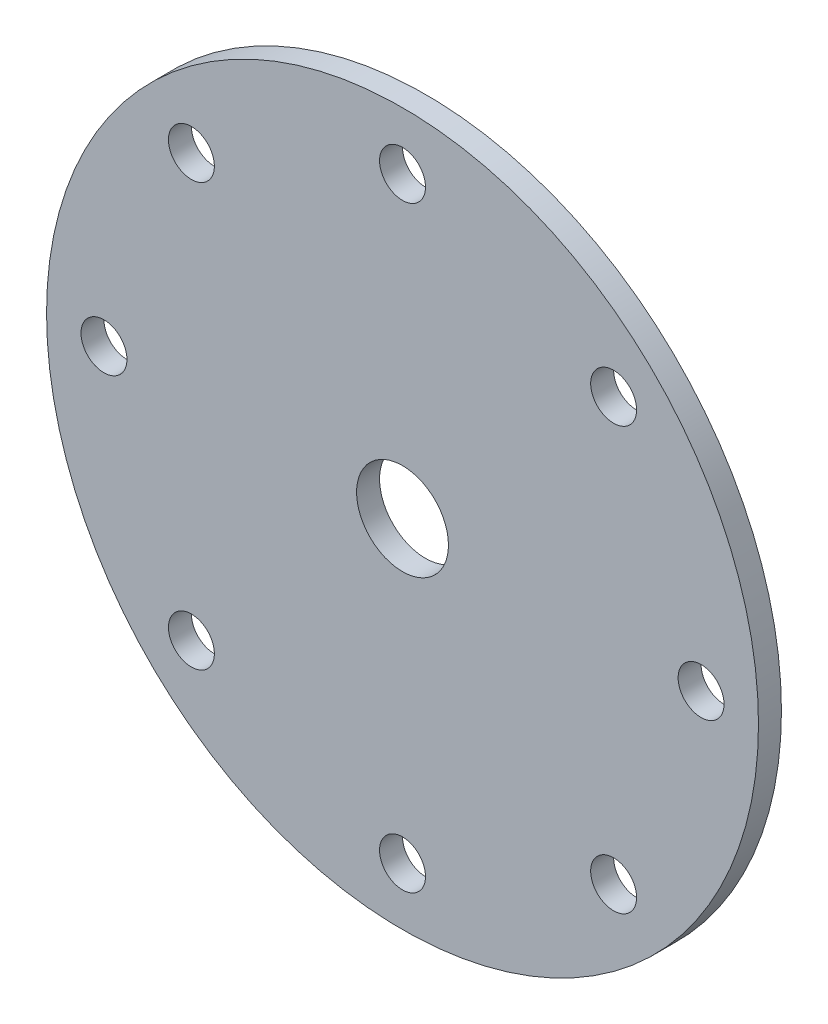
SolidWorks part; units mm, degrees
material "Plain Carbon Steel"
ref_plane "Front Plane" through (0, 0, 0) normal (0, 0, 1) x (1, 0, 0)
ref_plane "Top Plane" through (0, 0, 0) normal (0, 1, 0) x (1, 0, 0)
ref_plane "Right Plane" through (0, 0, 0) normal (1, 0, 0) x (0, 0, -1)
sketch "Sketch1" plane through (0, 0, 0) normal (0, 0, 1) x (1, 0, 0)
  line L0 (0, 98.425) -> (0, -98.425) construction
  line L1 (-98.425, 0) -> (98.425, 0) construction
  line L2 (-58.3717, 58.3717) -> (58.3717, -58.3717) construction
  line L3 (-58.3717, -58.3717) -> (58.3717, 58.3717) construction
  circle A0 centre (0, 0) radius 98.425
  circle A1 centre (0, 0) radius 12.7
  circle A2 centre (0, 82.55) radius 6.35
  circle A6 centre (58.3717, 58.3717) radius 6.35
  circle A7 centre (82.55, 0) radius 6.35
  circle A8 centre (58.3717, -58.3717) radius 6.35
  circle A9 centre (0, -82.55) radius 6.35
  circle A10 centre (-58.3717, -58.3717) radius 6.35
  circle A11 centre (-82.55, 0) radius 6.35
  circle A12 centre (-58.3717, 58.3717) radius 6.35
  point P26 (2.6773, -81.1549)
  dimension "D1" = 196.85
  dimension "D2" = 25.4
  dimension "D3" = 12.7
  dimension "D6" = 82.55
  dimension "D4" = 82.55
  dimension "D5" = 8
extrude "Rotor Disc" add sketch "Sketch1" along normal blind 6.35
